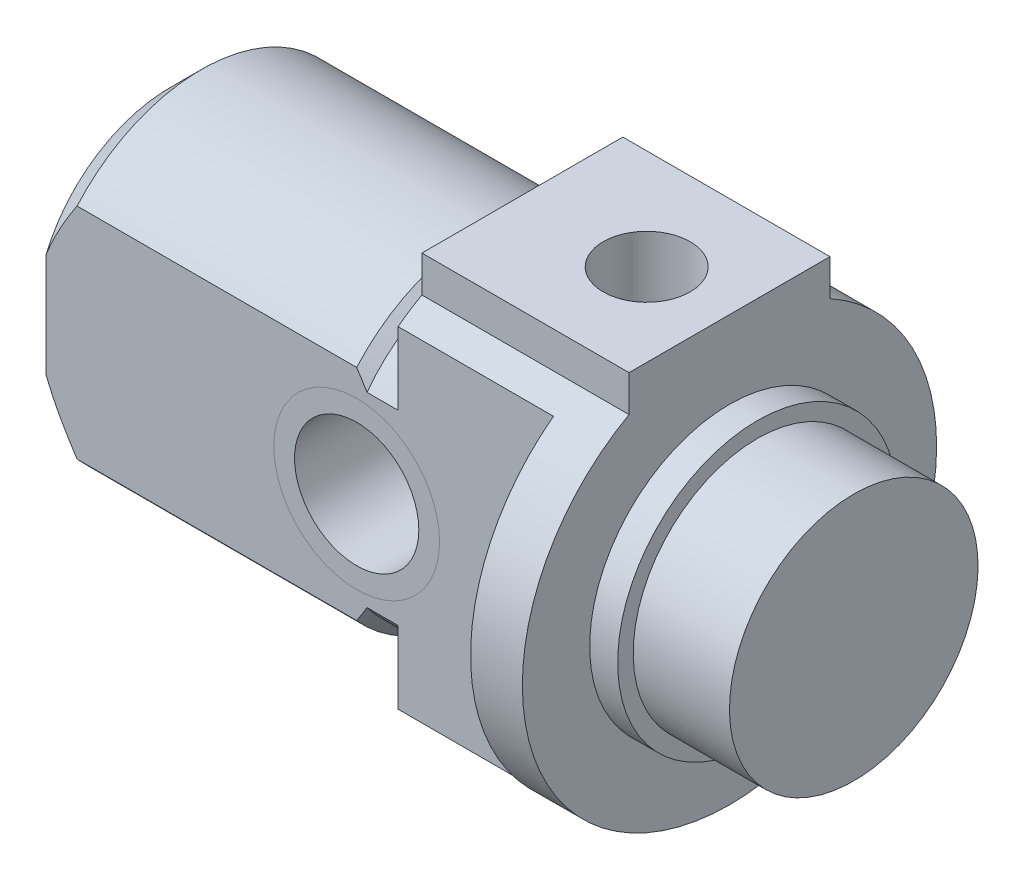
SolidWorks part; units mm, degrees
material "6061-T6 (SS)"
ref_plane "Front Plane" through (0, 0, 0) normal (0, 0, 1) x (1, 0, 0)
ref_plane "Top Plane" through (0, 0, 0) normal (0, 1, 0) x (1, 0, 0)
ref_plane "Right Plane" through (0, 0, 0) normal (1, 0, 0) x (0, 0, -1)
sketch "Sketch1" plane through (0, 0, 0) normal (1, 0, 0) x (0, 0, -1)
  line L0 (0, 0) -> (0, 17.9915) construction
  line L1 (-4.85, 8.7451) -> (-4.85, 10.5)
  line L2 (4.85, 8.7451) -> (4.85, 10.5)
  line L6 (-4.85, 10.5) -> (4.85, 10.5)
  arc A0 (-4.85, 8.7451) -> (4.85, 8.7451) centre (0, 0) ccw
  dimension "RM DIAD2" = 20
  dimension "RMD1" = 9.7
  dimension "RM HEOGHT D3" = 20.5
extrude "Boss-Extrude1" add sketch "Sketch1" along normal blind 33
sketch "Sketch2" plane through (0, 0, 0) normal (0, 0, 1) x (1, 0, 0)
  line L0 (27, 14) -> (27, 6.75)
  line L1 (27, 6.75) -> (28.35, 6.75)
  line L2 (28.35, 6.75) -> (28.35, 6)
  line L3 (28.35, 6) -> (33, 6)
  line L4 (33, -10) -> (33, 8.7451) construction
  line L5 (33, 6) -> (33, 14)
  line L6 (33, 0) -> (0, 0) construction
  line L7 (27, 14) -> (33, 14)
  line L8 (45.5, 0) -> (0, 0) construction
  dimension "BARREL STEP D1" = 13.5
  dimension "BARREL DIA D2" = 12
  dimension "BARREL GUIDED3" = 4.65
  dimension "BARREL EXTRA D4" = 6
  dimension "BARREL SUMA D5" = 8
revolve "Cut-Revolve1" cut sketch "Sketch2" angle 360 about L8
sketch "Sketch3" plane through (0, 0, 0) normal (0, 0, 1) x (1, 0, 0)
  line L0 (0, 0) -> (15.0791, 0) construction
  line L1 (0, 8.7451) -> (0, -10) construction
  line L2 (0, 8) -> (15, 8)
  line L3 (15, 8) -> (15.5, 7.5)
  line L4 (0, 8) -> (0, 16)
  line L5 (0, 16) -> (17, 16)
  line L6 (15.5, 7.5) -> (17, 7.5)
  line L7 (17, 7.5) -> (17, 16)
  line L10 (27, 0) -> (0, 0) construction
  dimension "THREAD SUMA D1" = 8
  dimension "THREAD DIA D2" = 16
  dimension "THREAD LENGTH D3" = 17
  dimension "THREAD ANGLED4" = 45
  dimension "THREAD GROOVE WIDTHD5" = 1.5
  dimension "THREAD GROOVE DIAD6" = 15
revolve "Cut-Revolve2" cut sketch "Sketch3" angle 360 about L0
cosmetic thread "Cosmetic Thread1" parameters "THREAD SIZE D2"=10.619
chamfer "Chamfer1" distance 1.5 angle 45 1 edges at (0, 0, 8)
hole_wizard "G1/8 Tapped Hole1" positions "Sketch5" profile "Sketch4" tap size "G1/8" standard "BSI"
sketch "Sketch5" plane through (0, 10.5, 0) normal (0, 1, 0) x (-1, 0, 0)
  line L0 (-28.35, 6.75) -> (-28.35, -6.75) construction
  line L6 (-15, 0) -> (-1.5, 0) construction
  point P0 (-23, 0)
  dimension "HOLE LOCATION D1" = 5.35
sketch "Sketch4" plane through (23, 10.5, 0) normal (1, 0, 0) x (0, 0, 1)
  line L0 (0, 0) -> (0, 12.2618)
  line L1 (0, 12.2618) -> (2.1, 11)
  line L2 (2.1, 11) -> (2.1, 0)
  line L5 (2.1, 0) -> (0, 0)
  line L10 (0, 12.2618) -> (-2.1, 11) construction
  line L11 (0, -6.35) -> (0, 107.95) construction
  dimension "Tap Drill Dia." = 4.2
  dimension "Tap Drill Depth" = 11
  dimension "Drill Angle" = 118
cosmetic thread "Hole Thread1" parameters "D1"=11, "D2"=5
sketch "Sketch6" plane through (33, 0, 0) normal (1, 0, 0) x (0, 0, -1)
  circle A0 centre (0, 0) radius 3
  dimension "PISTON ROD SIZE D1" = 6
extrude "Cut-Extrude1" [suppressed] cut sketch "Sketch6" against normal through all
sketch "Sketch7" plane through (28.35, 0, 0) normal (1, 0, 0) x (0, 0, -1)
  line L0 (-6, 8) -> (-6, -8)
  line L1 (-6, -8) -> (-21, -8)
  line L2 (-21, -8) -> (-21, 8)
  line L3 (-21, 8) -> (-6, 8)
  line L5 (0, -0.5) -> (0, 10.5) construction
  arc A0 (-4.85, 8.7451) -> (4.85, 8.7451) centre (0, 0) ccw construction
  dimension "D1" = 15
  dimension "SLOT D1" = 6
extrude "Cut-Extrude2" cut sketch "Sketch7" against normal through all from offset 3.85 offset against normal yes
mirror "Mirror1" about plane through (0, 0, 0) normal (0, 0, 1) of "Cut-Extrude2"
sketch "Sketch8" plane through (0, 0, 6) normal (0, 0, 1) x (1, 0, 0)
  line L0 (15, 0) -> (15.5, 0) construction
  line L1 (17, 0) -> (15.5, 0) construction
  line L2 (28.35, -6.75) -> (28.35, 6.75) construction
  circle A0 centre (15, 0) radius 4
  dimension "HOLE D1" = 8
  dimension "HOLE DIST D2" = 13.35
extrude "Cut-Extrude3" cut sketch "Sketch8" against normal through all
sketch "Sketch9" plane through (27, 0, 0) normal (1, 0, 0) x (0, 0, -1)
  line L0 (-4.3116, 7.9) -> (4.3116, 7.9)
  line L1 (-4.3116, -7.9) -> (4.3116, -7.9)
  line L2 (7.9, 4.3116) -> (7.9, -4.3116)
  line L3 (-7.9, 4.3116) -> (-7.9, -4.3116)
  line L4 (0, 0) -> (0, 7.9) construction
  line L5 (0, -0.5) -> (0, 10.5) construction
  line L6 (0, 0) -> (7.9, 0) construction
  line L7 (0, 9) -> (0, 10.5876) construction
  line L8 (9, 0) -> (10, 0) construction
  line L10 (-12.5, 12.5) -> (12.5, 12.5)
  line L11 (-12.5, 12.5) -> (-12.5, -12.5)
  line L12 (-12.5, -12.5) -> (12.5, -12.5)
  line L13 (12.5, 12.5) -> (12.5, -12.5)
  line L14 (-12.5, 12.5) -> (12.5, -12.5) construction
  line L15 (-12.5, -12.5) -> (12.5, 12.5) construction
  arc A0 (-4.3116, 7.9) -> (-7.9, 4.3116) centre (0, 0) ccw
  arc A1 (-4.85, 8.7451) -> (4.85, 8.7451) centre (0, 0) ccw construction
  arc A2 (7.9, 4.3116) -> (4.3116, 7.9) centre (0, 0) ccw
  arc A3 (4.3116, -7.9) -> (7.9, -4.3116) centre (0, 0) ccw
  arc A4 (-7.9, -4.3116) -> (-4.3116, -7.9) centre (0, 0) ccw
  dimension "D1" = 18
  dimension "D2" = 15.8
  dimension "D3" = 15.8
  dimension "D4" = 25
  dimension "D5" = 25
extrude "Cut-Extrude4" [suppressed] cut sketch "Sketch9" against normal through all
sketch "Sketch11" plane through (0, 0, 6) normal (0, 0, 1) x (1, 0, 0)
  circle A0 centre (15, 0) radius 4 construction
  circle A1 centre (15, 0) radius 4
  circle A2 centre (15, 0) radius 3
  dimension "D1" = 6
extrude "Boss-Extrude2" add sketch "Sketch11" against normal up to surface (12 mm away) separate body up to face at (11, 0, -6)
